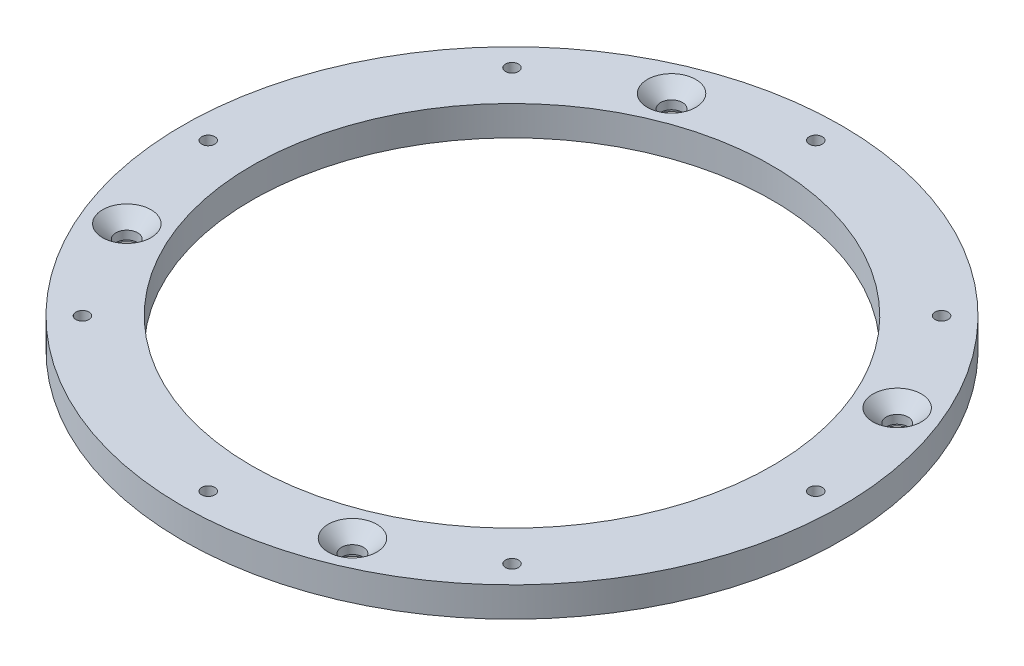
SolidWorks part; units mm, degrees
ref_plane "Front Plane" through (0, 0, 0) normal (0, 0, 1) x (1, 0, 0)
ref_plane "Top Plane" through (0, 0, 0) normal (0, 1, 0) x (1, 0, 0)
ref_plane "Right Plane" through (0, 0, 0) normal (1, 0, 0) x (0, 0, -1)
sketch "Sketch1" plane through (0, 0, 0) normal (0, 1, 0) x (1, 0, 0)
  circle A0 centre (0, 0) radius 131
  circle A1 centre (0, 0) radius 166
  dimension "D1" = 262
  dimension "D2" = 35
extrude "Boss-Extrude1" add sketch "Sketch1" along normal blind 15
ref_plane "Plane1" through (0, -5, 0) normal (0, -1, 0) x (-1, 0, 0)
hole_wizard "M6 Clearance Hole1" positions "Sketch2" profile "Sketch3" hole size "M6" standard "ISO" end condition through all
sketch "Sketch2" plane through (0, 0, 0) normal (0, -1, 0) x (-1, 0, 0)
  line L0 (0, 0) -> (0, 153) construction
  circle A0 centre (0, 0) radius 153
  point P0 (0, 153)
  point P10 (0, 0)
  dimension "D1" = 306
sketch "Sketch3" plane through (0, 0, -153) normal (1, 0, 0) x (0, 0, -1)
  line L0 (0, 0) -> (0, 15)
  line L1 (0, 15) -> (3.3, 15)
  line L2 (3.3, 15) -> (3.3, 0)
  line L5 (3.3, 0) -> (0, 0)
  line L11 (0, -6.35) -> (0, 107.95) construction
  dimension "Thru Hole Dia." = 6.6
  dimension "Thru Hole Depth" = 15
pattern_circular "CirPattern1" count 8 over 360 about axis through (0, 0, 0) along (0, 1, 0) of "M6 Clearance Hole1"
sketch "Sketch4" plane through (0, 0, 0) normal (0, -1, 0) x (1, 0, 0)
  line L0 (0, 0) -> (-108.1873, 108.1873) construction
  line L1 (-108.1873, 108.1873) -> (-153, 0) construction
  line L2 (-153, 0) -> (0, 0) construction
  line L3 (-153.364, 63.5254) -> (-137.1961, 56.8285) construction
  line L4 (-137.1961, 56.8285) -> (-121.0282, 50.1315) construction
  line L5 (-121.0282, 50.1315) -> (0, 0) construction
  circle A0 centre (-137.1961, 56.8285) radius 10
  circle A1 centre (0, 0) radius 148.5 construction
  circle A2 centre (0, 0) radius 166 construction
  circle A3 centre (0, 0) radius 131 construction
  dimension "D1" = 20
extrude "Cut-Extrude1" cut sketch "Sketch4" against normal blind 4
hole_wizard "CSK for M10 Hex Socket Countersunk Cap Screw1" positions "Sketch7" profile "Sketch8" countersink size "M10" standard "ISO" end condition through all
sketch "Sketch7" plane through (0, 15, 0) normal (0, 1, 0) x (1, 0, 0)
  point P0 (-137.1961, -56.8285)
sketch "Sketch8" plane through (-137.1961, 15, 56.8285) normal (1, 0, 0) x (0, 0, 1)
  line L0 (0, 0) -> (0, 15)
  line L1 (0, 15) -> (5.5, 15)
  line L2 (5.5, 15) -> (5.5, 6.7)
  line L3 (5.5, 6.7) -> (12.2, 0)
  line L5 (12.2, 0) -> (0, 0)
  line L6 (-5.5, 6.7) -> (-12.2, 0) construction
  line L11 (0, -6.35) -> (0, 107.95) construction
  dimension "Thru Hole Dia." = 11
  dimension "Thru Hole Depth" = 15
  dimension "Near C'Sink Dia." = 24.4
  dimension "Near C'Sink Angle" = 90
pattern_circular "CirPattern2" count 4 over 360 about axis through (0, 0, 0) along (0, 1, 0) of "Cut-Extrude1", "CSK for M10 Hex Socket Countersunk Cap Screw1"
